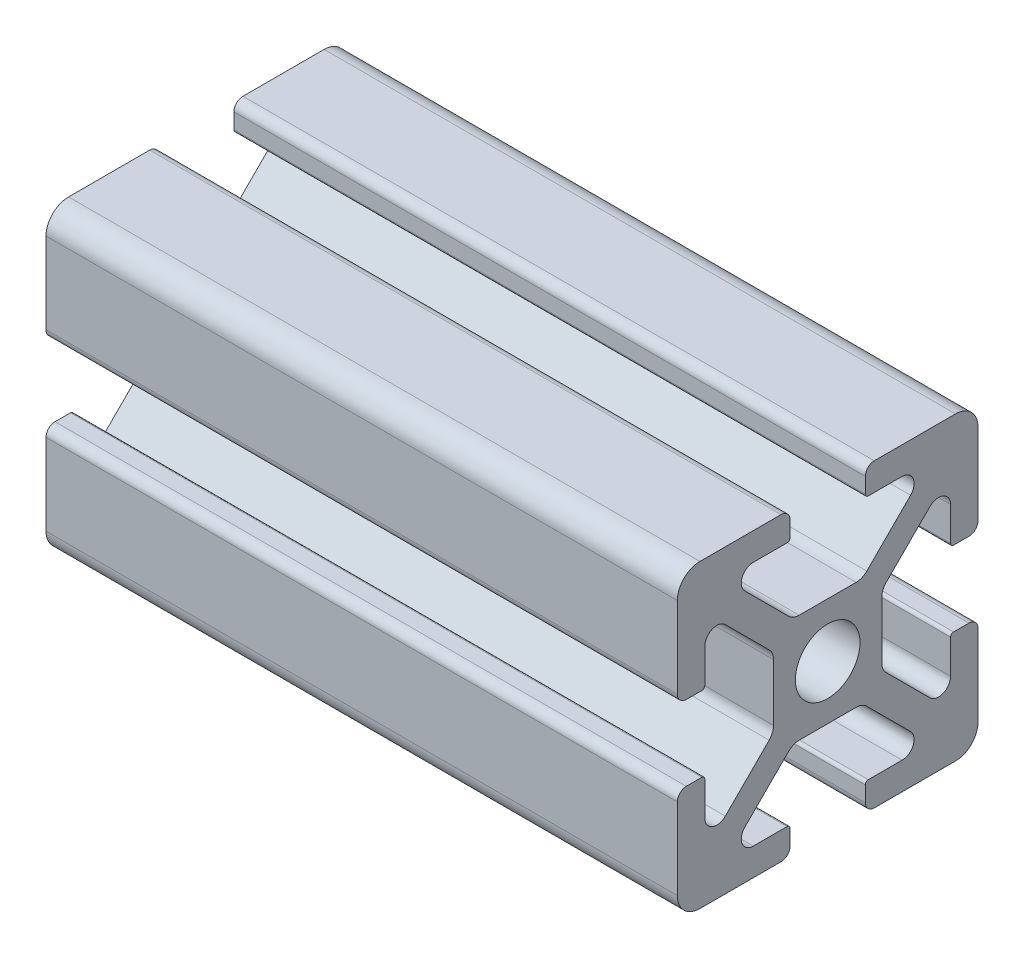
SolidWorks part; units mm, degrees
ref_plane "Front Plane" through (0, 0, 0) normal (0, 0, 1) x (1, 0, 0)
ref_plane "Top Plane" through (0, 0, 0) normal (0, 1, 0) x (1, 0, 0)
ref_plane "Right Plane" through (0, 0, 0) normal (1, 0, 0) x (0, 0, -1)
sketch "Sketch1" plane through (0, 0, 0) normal (1, 0, 0) x (0, 0, -1)
  line L0 (0, -10) -> (0, 10) construction
  line L1 (10, -10) -> (-10, -10)
  line L2 (10, -10) -> (10, 10)
  line L3 (10, 10) -> (0, 10)
  line L4 (-10, -10) -> (-10, 10)
  line L5 (10, -10) -> (-10, 10) construction
  line L6 (10, 10) -> (-10, -10) construction
  line L7 (10, 0) -> (-10, 0) construction
  line L8 (-2.5, 9.4) -> (-2.5, 8.3731)
  line L9 (-2.7, 8.1731) -> (-4.95, 8.1731)
  line L10 (-5.5157, 6.8075) -> (-2.6011, 3.8929)
  line L11 (-1.894, 3.6) -> (0, 3.6)
  line L12 (-5.3502, 4.0584) -> (-4.0584, 5.3502) construction
  line L13 (-3.825, 8.1731) -> (-3.825, 10) construction
  line L14 (-3.1, 10) -> (-10, 10)
  line L15 (-5.75, 7.3731) -> (5.75, 7.3731) construction
  circle A0 centre (0, 0) radius 2.15
  arc A1 (-4.95, 8.1731) -> (-5.5157, 6.8075) centre (-4.95, 7.3731) ccw
  arc A2 (-2.6011, 3.8929) -> (-1.894, 3.6) centre (-1.894, 4.6) ccw
  arc A3 (-2.5, 8.3731) -> (-2.7, 8.1731) centre (-2.7, 8.3731) cw
  arc A4 (-2.5, 9.4) -> (-3.1, 10) centre (-3.1, 9.4) ccw
  point P0 (0, 0)
  point P9 (0, 0)
  point P12 (0, 0)
  point P22 (-4.7043, 4.7043)
  point P32 (-2.5, 10)
  point P33 (-2.5, 8.8866)
  point P35 (-4.0584, 5.3502)
  point P37 (0, 7.3731)
  dimension "Center Hole Diameter" = 4.3
  dimension "D4" = 1
  dimension "D5" = 0.2
  dimension "D6" = 0.6
  dimension "D3" = 0.8
  dimension "Rail Height" = 20
  dimension "D7" = 6.4
  dimension "T Slot Width" = 5
  dimension "D10" = 10
  dimension "Rail Width" = 20
  dimension "D2" = 11.5
sketch "Sketch2" plane through (0, 0, 0) normal (0, 0, 1) x (1, 0, 0)
  line L0 (-132.4, 10) -> (-132.4, -10) construction
  line L1 (152.4, -10) -> (-152.4, -10) construction
  line L2 (152.4, -10) -> (152.4, 10) construction
  line L3 (152.4, 10) -> (-152.4, 10) construction
  line L4 (-152.4, -10) -> (-152.4, 10) construction
  line L5 (152.4, -10) -> (-152.4, 10) construction
  line L6 (152.4, 10) -> (-152.4, -10) construction
  line L7 (132.4, 10) -> (132.4, -10) construction
  point P0 (0, 0)
  point P12 (132.4, 0)
  dimension "Length" = 304.8
  dimension "D1" = 20
  dimension "D2" = 20
sketch "Sketch3" plane through (0, 0, 0) normal (1, 0, 0) x (0, 0, -1)
  line L0 (-5.5157, 6.8075) -> (-2.6011, 3.8929) construction
  line L5 (-3.1, 10) -> (-10, 10) construction
  line L6 (-2.5, 9.4) -> (-2.5, 8.3731) construction
  line L7 (-2.7, 8.1731) -> (-4.95, 8.1731) construction
  line L8 (-1.894, 3.6) -> (0, 3.6) construction
  line L9 (-5.5157, 6.8075) -> (-2.6011, 3.8929)
  line L10 (-10, 10) -> (0, 0) construction
  line L12 (-3.6, 1.894) -> (-3.6, 0)
  line L13 (-8.1731, 2.7) -> (-8.1731, 4.95)
  line L14 (-3.1, 10) -> (-8.5, 10)
  line L15 (-2.5, 9.4) -> (-2.5, 8.3731)
  line L16 (-2.7, 8.1731) -> (-4.95, 8.1731)
  line L17 (-1.894, 3.6) -> (0, 3.6)
  line L18 (-9.4, 2.5) -> (-8.3731, 2.5)
  line L19 (-10, 3.1) -> (-10, 8.5)
  line L20 (-6.8075, 5.5157) -> (-3.8929, 2.6011)
  line L21 (-3.6, 0) -> (-2.15, 0)
  line L22 (0, 3.6) -> (0, 2.15)
  arc A0 (-2.5, 9.4) -> (-3.1, 10) centre (-3.1, 9.4) ccw construction
  arc A1 (-2.7, 8.1731) -> (-2.5, 8.3731) centre (-2.7, 8.3731) ccw construction
  arc A2 (-4.95, 8.1731) -> (-5.5157, 6.8075) centre (-4.95, 7.3731) ccw construction
  arc A3 (-2.6011, 3.8929) -> (-1.894, 3.6) centre (-1.894, 4.6) ccw construction
  arc A4 (-2.5, 9.4) -> (-3.1, 10) centre (-3.1, 9.4) ccw
  arc A5 (-2.7, 8.1731) -> (-2.5, 8.3731) centre (-2.7, 8.3731) ccw
  arc A6 (-4.95, 8.1731) -> (-5.5157, 6.8075) centre (-4.95, 7.3731) ccw
  arc A7 (-2.6011, 3.8929) -> (-1.894, 3.6) centre (-1.894, 4.6) ccw
  arc A8 (-3.8929, 2.6011) -> (-3.6, 1.894) centre (-4.6, 1.894) cw
  arc A9 (-8.1731, 4.95) -> (-6.8075, 5.5157) centre (-7.3731, 4.95) cw
  arc A10 (-8.1731, 2.7) -> (-8.3731, 2.5) centre (-8.3731, 2.7) cw
  arc A11 (-9.4, 2.5) -> (-10, 3.1) centre (-9.4, 3.1) cw
  circle A12 centre (0, 0) radius 2.15 construction
  arc A13 (0, 2.15) -> (-2.15, 0) centre (0, 0) ccw
  arc A14 (-10, 8.5) -> (-8.5, 10) centre (-8.5, 8.5) cw
  dimension "D1" = 1.5
extrude "Boss-Extrude1" add sketch "Sketch3" against normal blind 42
mirror "Mirror1" about plane through (0, 0, 0) normal (0, 1, 0) of bodies 104
mirror "Mirror2" about plane through (0, 0, 0) normal (0, 0, 1) of bodies 105
equation "\"D10@Sketch1\" = \"Rail Height@Sketch1\" / 2"
equation "\"D2@Sketch2\"=\"D1@Sketch2\""
